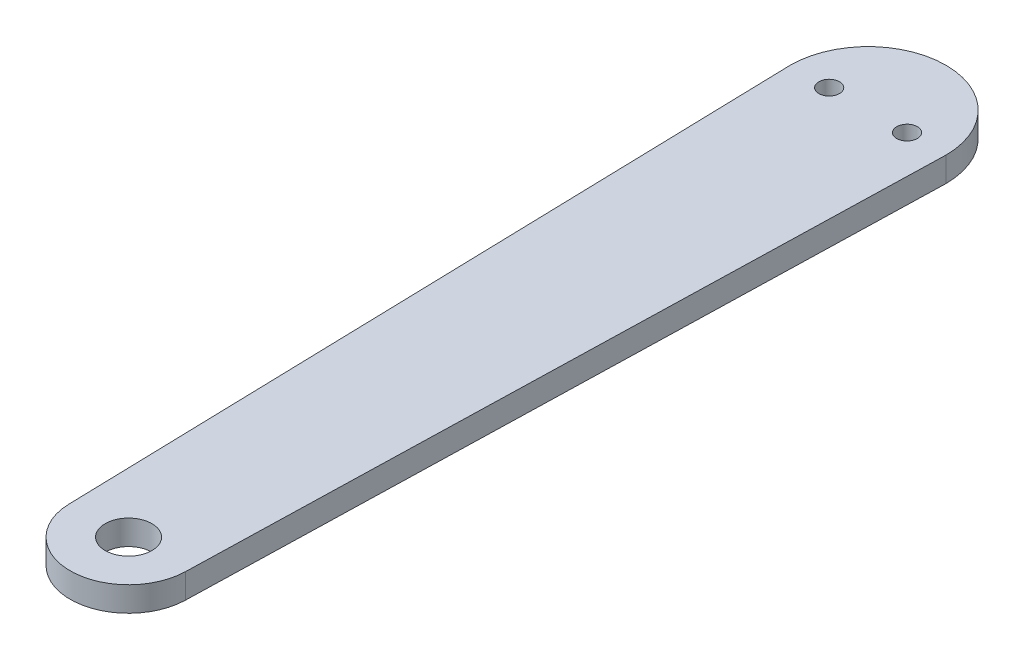
SolidWorks part; units mm, degrees
material "1060 Alloy"
ref_plane "Front Plane" through (0, 0, 0) normal (0, 0, 1) x (1, 0, 0)
ref_plane "Top Plane" through (0, 0, 0) normal (0, 1, 0) x (1, 0, 0)
ref_plane "Right Plane" through (0, 0, 0) normal (1, 0, 0) x (0, 0, -1)
sketch "Sketch1" plane through (0, 0, 0) normal (0, 1, 0) x (1, 0, 0)
  line L0 (-20, 0) -> (-14.9948, -190.3942)
  line L1 (20, 0) -> (14.9948, -190.3942)
  line L2 (-20, 0) -> (0, 0) construction
  line L3 (0, 0) -> (20, 0) construction
  arc A0 (-20, 0) -> (20, 0) centre (0, 0) cw
  arc A1 (-14.9948, -190.3942) -> (14.9948, -190.3942) centre (0, -190) ccw
  circle A2 centre (0, -190) radius 6
  dimension "D1" = 20
  dimension "D2" = 15
  dimension "D4" = 12
  dimension "D3" = 190
extrude "Boss-Extrude1" add sketch "Sketch1" along normal blind 6.35
sketch "Sketch4" plane through (0, 6.35, 0) normal (0, 1, 0) x (1, 0, 0)
  line L0 (0, 0) -> (-10, 0) construction
  line L1 (0, 0) -> (10, 0) construction
  dimension "D1" = 10
hole_wizard "M5 Clearance Hole1" positions "Sketch5" profile "Sketch6" hole size "M5" standard "ANSI Metric" end condition through all
sketch "Sketch5" plane through (0, 6.35, 0) normal (0, 1, 0) x (1, 0, 0)
  point P0 (-10, 0)
  point P3 (10, 0)
sketch "Sketch6" plane through (-10, 6.35, 0) normal (1, 0, 0) x (0, 0, 1)
  line L0 (0, 0) -> (0, 6.35)
  line L1 (0, 6.35) -> (2.65, 6.35)
  line L2 (2.65, 6.35) -> (2.65, 0)
  line L5 (2.65, 0) -> (0, 0)
  line L11 (0, -6.35) -> (0, 107.95) construction
  dimension "Thru Hole Dia." = 5.3
  dimension "Thru Hole Depth" = 6.35
equation "\"tubeOutDiameter\" = 35mm"
equation "\"wheelShaftDiameter\"= 12mm"
equation "\"wheelThickness\"= 135mm"
equation "\"BearingDiameter\"= 20mm"
equation "\"BearingThickness\"= 10mm"
equation "\"frontShaftDiameter\"= 20mm"
